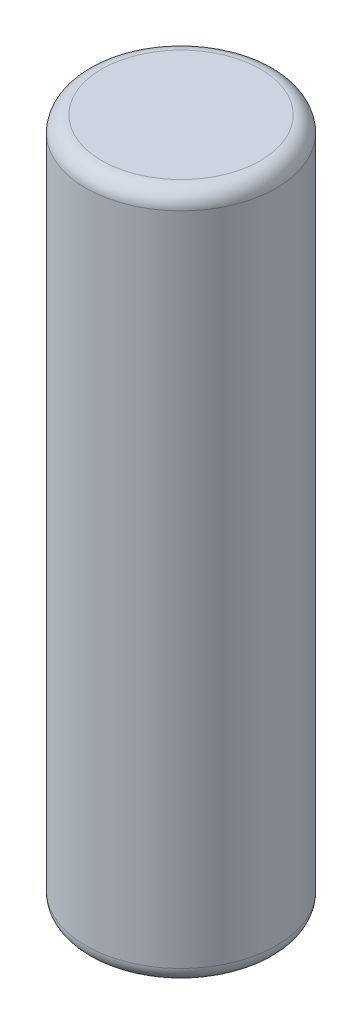
SolidWorks part; units mm, degrees
ref_plane "Front Plane" through (0, 0, 0) normal (0, 0, 1) x (1, 0, 0)
ref_plane "Top Plane" through (0, 0, 0) normal (0, 1, 0) x (1, 0, 0)
ref_plane "Right Plane" through (0, 0, 0) normal (1, 0, 0) x (0, 0, -1)
sketch "Sketch2" plane through (0, 0, 0) normal (0, 1, 0) x (1, 0, 0)
  circle A0 centre (0, 0) radius 9
  dimension "D1" = 18
extrude "Boss-Extrude1" add sketch "Sketch2" along normal blind 65
fillet "Fillet1" radius 1.5 2 edges at (0, 0, 9) (0, 65, 9)
